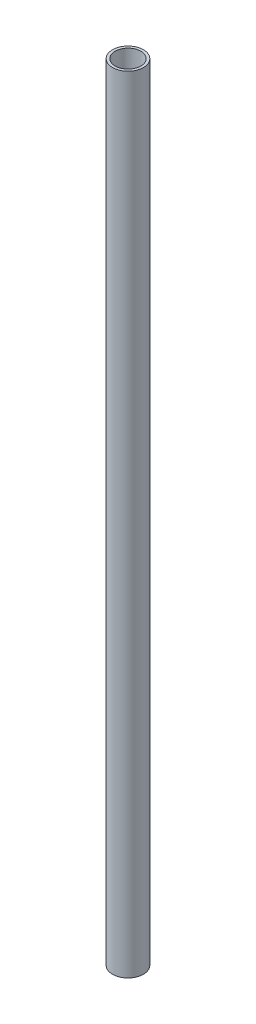
SolidWorks part; units mm, degrees
material "6061 Alloy"
ref_plane "Front Plane" through (0, 0, 0) normal (0, 0, 1) x (1, 0, 0)
ref_plane "Top Plane" through (0, 0, 0) normal (0, 1, 0) x (1, 0, 0)
ref_plane "Right Plane" through (0, 0, 0) normal (1, 0, 0) x (0, 0, -1)
sketch "Sketch1" plane through (0, 0, 0) normal (0, 1, 0) x (1, 0, 0)
  circle A0 centre (0, 0) radius 6
  circle A1 centre (0, 0) radius 5
  dimension "D1" = 12
  dimension "D2" = 10
extrude "Boss-Extrude1" add sketch "Sketch1" along normal blind 305
